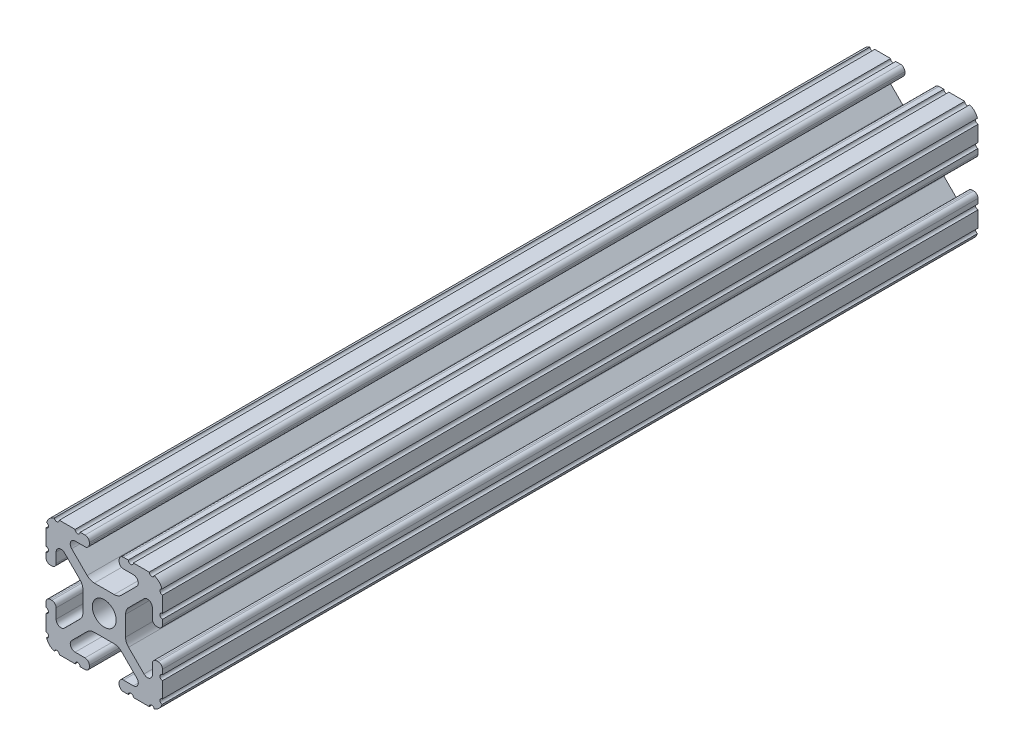
SolidWorks part; units mm, degrees
ref_plane "Front Plane" through (0, 0, 0) normal (0, 0, 1) x (1, 0, 0)
ref_plane "Top Plane" through (0, 0, 0) normal (0, 1, 0) x (1, 0, 0)
ref_plane "Right Plane" through (0, 0, 0) normal (1, 0, 0) x (0, 0, -1)
sketch "Sketch2" plane through (0, 0, 0) normal (0, 0, 1) x (1, 0, 0)
  line L0 (0, 12.7) -> (0, -12.7) construction
  line L1 (-12.7, 0) -> (12.7, 0) construction
  line L2 (3.2512, -12.7) -> (12.7, -12.7)
  line L3 (12.7, -12.7) -> (12.7, -3.2512)
  line L4 (3.2512, -12.7) -> (3.2512, -10.4902)
  line L5 (3.2512, -10.4902) -> (8.9276, -10.4902)
  line L6 (8.9276, -10.4902) -> (3.0856, -4.6482)
  line L7 (0, 0) -> (12.7, -12.7) construction
  line L8 (12.7, -3.2512) -> (10.4902, -3.2512)
  line L9 (10.4902, -3.2512) -> (10.4902, -8.9276)
  line L10 (10.4902, -8.9276) -> (4.6482, -3.0856)
  circle A0 centre (0, 0) radius 2.6035
  arc A1 (6.3485, -10.4902) -> (7.1039, -8.6665) centre (6.3485, -9.4219) ccw construction
  point P8 (0, -4.6482)
  dimension "Center Hole Diameter" = 5.207
  dimension "Rail Height" = 25.4
  dimension "Rail Width" = 25.4
  dimension "T-Slot Width" = 6.5024
  dimension "Slot Inner Width" = 14.8336
  dimension "Thickness" = 2.2098
  dimension "Slot Depth" = 5.842
  dimension "D1" = 2.2098
sketch "Sketch3" plane through (0, 0, 0) normal (1, 0, 0) x (0, 0, -1)
  line L0 (-88.9, -12.7) -> (88.9, -12.7) construction
  line L1 (-63.5, 0) -> (63.5, 0) construction
  dimension "Length" = 177.8
  dimension "D1" = 25.4
sketch "Sketch4" plane through (0, 0, 0) normal (0, 0, 1) x (1, 0, 0)
  line L0 (4.1904, -12.7) -> (10.1173, -12.7)
  line L1 (3.2512, -12.7) -> (12.7, -12.7) construction
  line L2 (3.2512, -12.7) -> (3.2512, -10.4902) construction
  line L3 (3.2512, -10.4902) -> (8.9276, -10.4902) construction
  line L4 (3.2512, -11.4294) -> (3.2512, -11.7608)
  line L5 (4.1904, -10.4902) -> (6.3485, -10.4902)
  line L6 (0, -4.6482) -> (2.164, -4.6482)
  line L7 (8.9276, -10.4902) -> (3.0856, -4.6482) construction
  line L8 (3.7373, -5.2999) -> (7.1039, -8.6665)
  line L9 (12.7, -12.7) -> (12.7, -3.2512) construction
  line L10 (10.4902, -8.9276) -> (4.6482, -3.0856) construction
  line L11 (10.4902, -3.2512) -> (10.4902, -8.9276) construction
  line L12 (10.4902, -6.3485) -> (10.4902, -4.1904)
  line L13 (12.7, -3.2512) -> (10.4902, -3.2512) construction
  line L14 (11.4294, -3.2512) -> (11.7608, -3.2512)
  line L15 (12.7, -4.1904) -> (12.7, -10.1173)
  line L16 (8.6665, -7.1039) -> (5.2999, -3.7373)
  line L17 (4.6482, 0) -> (4.6482, -2.164)
  line L18 (-12.7, 0) -> (12.7, 0) construction
  line L19 (0, -4.6482) -> (0, -2.6035)
  line L20 (0, 12.7) -> (0, -12.7) construction
  line L21 (4.6482, 0) -> (2.6035, 0)
  arc A0 (3.2512, -11.7608) -> (4.1904, -12.7) centre (4.1904, -11.7608) ccw
  arc A2 (3.2512, -11.4294) -> (4.1904, -10.4902) centre (4.1904, -11.4294) cw
  arc A3 (6.3485, -10.4902) -> (7.1039, -8.6665) centre (6.3485, -9.4219) ccw
  arc A4 (2.164, -4.6482) -> (3.7373, -5.2999) centre (2.164, -6.8732) cw
  arc A5 (10.1173, -12.7) -> (12.7, -10.1173) centre (10.1173, -10.1173) ccw
  arc A6 (8.6665, -7.1039) -> (10.4902, -6.3485) centre (9.4219, -6.3485) ccw
  arc A7 (10.4902, -4.1904) -> (11.4294, -3.2512) centre (11.4294, -4.1904) cw
  arc A8 (11.7608, -3.2512) -> (12.7, -4.1904) centre (11.7608, -4.1904) cw
  arc A9 (5.2999, -3.7373) -> (4.6482, -2.164) centre (6.8732, -2.164) cw
  circle A10 centre (0, 0) radius 2.6035 construction
  arc A11 (0, -2.6035) -> (2.6035, 0) centre (0, 0) ccw
  dimension "D1" = 2.5827
  dimension "D2" = 2.225
  dimension "D3" = 0.9392
extrude "Boss-Extrude1" add sketch "Sketch4" along normal mid plane 177.8
sketch "Sketch5" plane through (0, 0, 0) normal (0, 0, 1) x (1, 0, 0)
  line L0 (3.2512, -12.7) -> (12.7, -12.7) construction
  line L1 (4.1904, -10.4902) -> (6.3485, -10.4902) construction
  line L3 (0, 0) -> (12.7, -12.7) construction
  line L4 (6.3485, -10.4902) -> (6.3485, -12.7) construction
  line L5 (8.9276, -10.4902) -> (3.0856, -4.6482) construction
  circle A0 centre (10.3562, -12.7) radius 0.5524
  circle A1 centre (5.796, -12.7) radius 0.5524
  circle A2 centre (12.7, -10.3562) radius 0.5524
  circle A3 centre (12.7, -5.796) radius 0.5524
  point P10 (5.2694, -10.4902)
  point P12 (9.4219, -6.3485)
  dimension "D1" = 1.1049
extrude "Cut-Extrude1" cut sketch "Sketch5" against normal through all both and the other way through all
mirror "Mirror1" about plane through (0, 0, 0) normal (1, 0, 0) of bodies 137 134
mirror "Mirror2" about plane through (0, 0, 0) normal (0, 1, 0) of bodies 135
equation "\"D1@Boss-Extrude1\"=\"Length@Sketch3\""
equation "\"D1@Sketch2\"=\"Thickness@Sketch2\""
equation "\"D2@Sketch4\"=\"Slot Inner Width@Sketch2\"*0.15"
equation "\"D1@Sketch4\"=\"D3@Sketch4\"*2.75"
equation "\"D3@Sketch4\"=\"Thickness@Sketch2\"*0.425"
equation "\"D1@Sketch5\"=\"Thickness@Sketch2\"*0.5"
